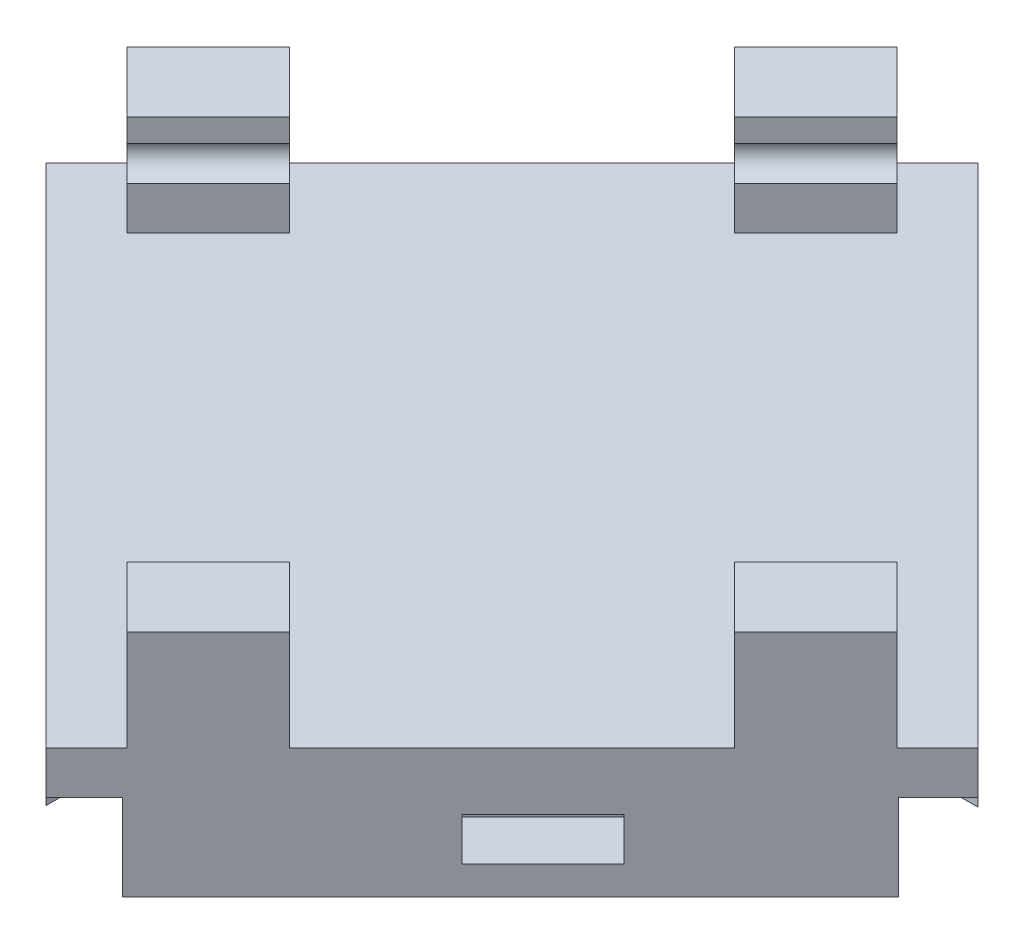
SolidWorks part; units mm, degrees
ref_plane "Front Plane" through (0, 0, 0) normal (0, 0, 1) x (1, 0, 0)
ref_plane "Top Plane" through (0, 0, 0) normal (0, 1, 0) x (1, 0, 0)
ref_plane "Right Plane" through (0, 0, 0) normal (1, 0, 0) x (0, 0, -1)
sketch "Sketch2" plane through (0, 0, 0) normal (0, 1, 0) x (1, 0, 0)
  line L0 (-4.5675, 15.8206) -> (13.1101, -1.8571)
  line L1 (-3.1429, -18.1101) -> (-20.8206, -0.4325)
  line L5 (-3.1429, -18.1101) -> (13.1101, -1.8571)
  line L7 (-4.5675, 15.8206) -> (-20.8206, -0.4325)
extrude "Boss-Extrude2" add sketch "Sketch2" along normal blind 4.5
sketch "Sketch4" plane through (0, 0, 0) normal (0, 1, 0) x (1, 0, 0)
  line L0 (-18.0083, -3.2448) -> (-5.9052, -3.2448)
  line L1 (-20.8206, -0.4325) -> (-3.1429, -18.1101) construction
  line L2 (-5.9052, -15.3478) -> (-5.9052, -3.2448)
  line L3 (-1.8052, -3.2448) -> (-1.8052, -16.7724)
  line L4 (-3.1429, -18.1101) -> (13.1101, -1.8571) construction
  line L5 (-5.9052, -15.3478) -> (-3.1429, -18.1101)
  line L6 (-3.1429, -18.1101) -> (-1.8052, -16.7724)
  line L7 (-1.8052, -3.2448) -> (11.7224, -3.2448)
  line L8 (11.7224, -3.2448) -> (13.1101, -1.8571)
  line L9 (13.1101, -1.8571) -> (10.3978, 0.8552)
  line L10 (13.1101, -1.8571) -> (-4.5675, 15.8206) construction
  line L11 (-1.8322, 0.8552) -> (10.3978, 0.8552)
  line L12 (-1.8322, 0.8552) -> (-1.9961, 13.2491)
  line L13 (-5.9052, 14.4829) -> (-5.9052, 0.8552)
  line L14 (-4.5675, 15.8206) -> (-5.9052, 14.4829)
  line L15 (-4.5675, 15.8206) -> (-20.8206, -0.4325) construction
  line L16 (-5.9052, 0.8552) -> (-5.8915, 0.9778)
  line L17 (-5.9052, 0.8552) -> (-19.5329, 0.8552)
  line L18 (-19.5329, 0.8552) -> (-20.8206, -0.4325)
  line L19 (-20.8206, -0.4325) -> (-18.0083, -3.2448)
  line L20 (-1.9961, 13.2491) -> (-4.5675, 15.8206)
  point P2 (-3.8552, -1.1948)
  point P21 (-6.1654, -1.7695)
  dimension "D1" = 2.05
  dimension "D2" = 2.05
  dimension "D3" = 2.05
  dimension "D4" = 2.05
  dimension "D5" = 2.05
  dimension "D6" = 2.05
  dimension "D7" = 2.05
  dimension "D8" = 2.05
extrude "Cut-Extrude1" cut sketch "Sketch4" along normal blind 3
ref_plane "Plane2" through (0, 4.5, 0) normal (0, 1, 0) x (1, 0, 0)
sketch "Sketch5" plane through (0, 4.5, 0) normal (0, 1, 0) x (1, 0, 0)
  line L0 (8.8675, -6.0997) -> (11.6959, -3.2713)
  line L1 (11.6959, -3.2713) -> (9.5746, -1.15)
  line L2 (9.5746, -1.15) -> (6.7462, -3.9784)
  line L3 (8.8675, -6.0997) -> (6.7462, -3.9784)
  line L4 (13.1101, -1.8571) -> (-4.5675, 15.8206) construction
  line L5 (-3.1429, -18.1101) -> (13.1101, -1.8571) construction
  line L6 (-6.6889, 9.4566) -> (-3.8604, 12.2851)
  line L7 (-3.8604, 12.2851) -> (-5.9818, 14.4064)
  line L8 (-5.9818, 14.4064) -> (-8.8102, 11.578)
  line L9 (-8.8102, 11.578) -> (-6.6889, 9.4566)
  line L10 (-17.2851, -1.1396) -> (-14.4566, 1.6889)
  line L11 (-14.4566, 1.6889) -> (-16.578, 3.8102)
  line L12 (-16.578, 3.8102) -> (-19.4064, 0.9818)
  line L13 (-19.4064, 0.9818) -> (-17.2851, -1.1396)
  line L14 (-1.7287, -16.6959) -> (1.0997, -13.8675)
  line L15 (1.0997, -13.8675) -> (-1.0216, -11.7462)
  line L16 (-1.0216, -11.7462) -> (-3.85, -14.5746)
  line L17 (-3.85, -14.5746) -> (-1.7287, -16.6959)
  line L18 (-4.5675, 15.8206) -> (-20.8206, -0.4325) construction
  line L19 (-20.8206, -0.4325) -> (-3.1429, -18.1101) construction
  dimension "D1" = 3
  dimension "D2" = 4
  dimension "D3" = 2
  dimension "D4" = 3
  dimension "D5" = 4
  dimension "D6" = 3
  dimension "D7" = 3
  dimension "D8" = 3
  dimension "D9" = 4
  dimension "D10" = 3
  dimension "D11" = 3
  dimension "D12" = 4
  dimension "D13" = 3
  dimension "D14" = 2
  dimension "D15" = 2
  dimension "D16" = 2
extrude "Boss-Extrude3" add sketch "Sketch5" along normal blind 3.5
ref_plane "Plane3" through (4.2123, 0, -4.2123) normal (0.7071, 0, -0.7071) x (-0.7071, 0, -0.7071)
sketch "Sketch6" plane through (4.2123, 0, -4.2123) normal (0.7071, 0, -0.7071) x (-0.7071, 0, -0.7071)
  line L1 (-7.5834, 8) -> (-7.5834, 4.5) construction
  arc A0 (-7.5834, 7.2) -> (-7.5834, 6) centre (-7.5834, 6.6) ccw
  dimension "D1" = 0.6
  dimension "D2" = 1.5
  dimension "D3" = 0
extrude "Cut-Extrude2" cut sketch "Sketch6" against normal through all and the other way through all
ref_plane "Plane4" through (4.2123, 0, -4.2123) normal (0.7071, 0, -0.7071) x (-0.7071, 0, -0.7071)
sketch "Sketch7" plane through (4.2123, 0, -4.2123) normal (0.7071, 0, -0.7071) x (-0.7071, 0, -0.7071)
  line L0 (11.4166, 8) -> (11.4166, 4.5) construction
  line L1 (11.4166, 7.2) -> (11.4166, 6)
  arc A0 (11.4166, 7.2) -> (11.4166, 6) centre (11.4166, 6.6) cw
  dimension "D1" = 0.6
  dimension "D2" = 1.5
  dimension "D3" = 0
extrude "Cut-Extrude5" cut sketch "Sketch7" against normal through all
ref_plane "Plane5" through (5.6265, 0, -5.6265) normal (0.7071, 0, -0.7071) x (-0.7071, 0, -0.7071)
sketch "Sketch10" plane through (5.6265, 0, -5.6265) normal (0.7071, 0, -0.7071) x (-0.7071, 0, -0.7071)
  line L0 (-6.7476, 0) -> (10.78, 0) construction
  line L1 (0.015, 2.5) -> (4.015, 2.5)
  line L2 (0.015, 2.5) -> (0.015, 1)
  line L3 (0.015, 1) -> (4.015, 1)
  line L4 (4.015, 2.5) -> (4.015, 1)
  line L5 (10.78, 3) -> (10.78, 0) construction
  point P6 (2.015, 1)
  dimension "D1" = 1
  dimension "D2" = 4
  dimension "D3" = 1.5
  dimension "D4" = 8.765
extrude "Cut-Extrude6" cut sketch "Sketch10" against normal blind 2
ref_plane "Plane6" through (-10.6265, 0, 10.6265) normal (-0.7071, 0, 0.7071) x (0.7071, 0, 0.7071)
sketch "Sketch11" plane through (-10.6265, 0, 10.6265) normal (-0.7071, 0, 0.7071) x (0.7071, 0, 0.7071)
  line L0 (-10.4394, 0) -> (6.6769, 0) construction
  line L1 (-4.0881, 2.5) -> (-0.0881, 2.5)
  line L2 (-4.0881, 2.5) -> (-4.0881, 1)
  line L3 (-4.0881, 1) -> (-0.0881, 1)
  line L4 (-0.0881, 2.5) -> (-0.0881, 1)
  point P6 (-2.0881, 1)
  dimension "D1" = 1.5
  dimension "D2" = 4
  dimension "D3" = 1
  dimension "D4" = 8.765
extrude "Cut-Extrude7" cut sketch "Sketch11" against normal blind 2
ref_plane "Plane7" through (7.4836, 0, 7.4836) normal (0.7071, 0, 0.7071) x (0.7071, 0, -0.7071)
sketch "Sketch12" plane through (7.4836, 0, 7.4836) normal (0.7071, 0, 0.7071) x (0.7071, 0, -0.7071)
  line L0 (-13.1364, 0) -> (5.9946, 0) construction
  line L1 (-4.7704, 2.5) -> (-0.7704, 2.5)
  line L2 (-4.7704, 2.5) -> (-4.7704, 1)
  line L3 (-4.7704, 1) -> (-0.7704, 1)
  line L4 (-0.7704, 2.5) -> (-0.7704, 1)
  point P6 (-2.7704, 1)
  dimension "D1" = 1.5
  dimension "D2" = 4
  dimension "D3" = 1
  dimension "D4" = 8.765
extrude "Cut-Extrude8" cut sketch "Sketch12" against normal blind 2
ref_plane "Plane8" through (-10.1941, 0, -10.1941) normal (-0.7071, 0, -0.7071) x (-0.7071, 0, 0.7071)
sketch "Sketch13" plane through (-10.1941, 0, -10.1941) normal (-0.7071, 0, -0.7071) x (-0.7071, 0, 0.7071)
  line L0 (-6.0653, 0) -> (13.2071, 0) construction
  line L1 (2.4421, 2.5) -> (6.4421, 2.5)
  line L2 (2.4421, 2.5) -> (2.4421, 1)
  line L3 (2.4421, 1) -> (6.4421, 1)
  line L4 (6.4421, 2.5) -> (6.4421, 1)
  point P6 (4.4421, 1)
  dimension "D1" = 4
  dimension "D2" = 1.5
  dimension "D3" = 1
  dimension "D4" = 8.765
extrude "Cut-Extrude9" cut sketch "Sketch13" against normal blind 2
